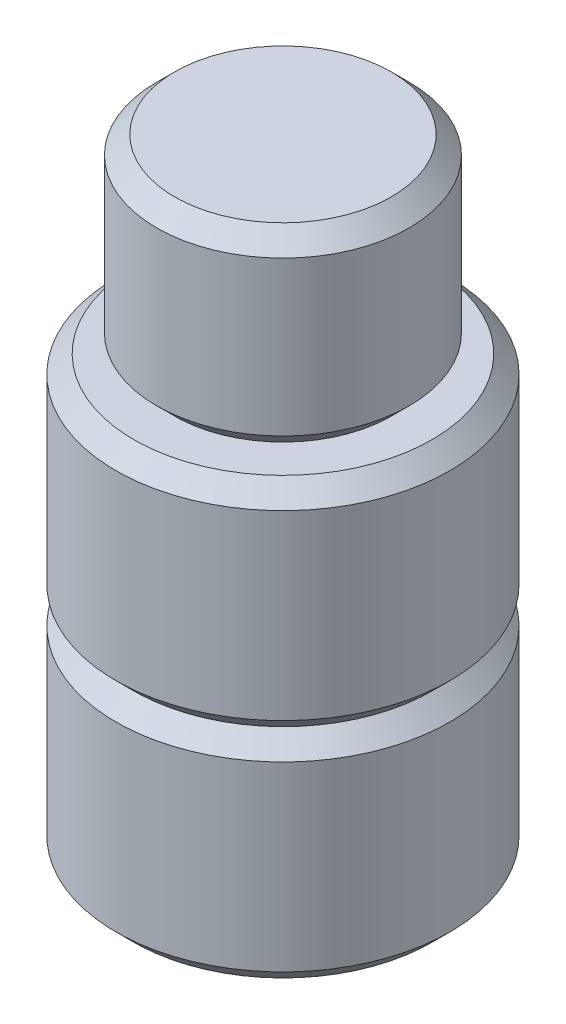
SolidWorks part; units mm, degrees
ref_plane "Front" through (0, 0, 0) normal (0, 0, 1) x (1, 0, 0)
ref_plane "Top" through (0, 0, 0) normal (0, 1, 0) x (1, 0, 0)
ref_plane "Right" through (0, 0, 0) normal (1, 0, 0) x (0, 0, -1)
sketch "Sketch1" plane through (0, 0, 0) normal (0, 0, 1) x (1, 0, 0)
  line L0 (0, 0) -> (0, 69.83) construction
  line L1 (0, 0) -> (16.65, 0)
  line L2 (16.65, 0) -> (18.65, 2)
  line L3 (18.65, 2) -> (18.65, 22.31)
  line L4 (18.65, 22.31) -> (16.65, 24.31)
  line L5 (16.65, 24.31) -> (18.65, 26.31)
  line L6 (18.65, 26.31) -> (18.65, 46.62)
  line L7 (18.65, 46.62) -> (16.65, 48.62)
  line L8 (16.65, 24.31) -> (0, 24.31) construction
  line L9 (16.65, 48.62) -> (0, 48.62) construction
  line L10 (16.65, 48.62) -> (12.1, 48.62)
  line L11 (12.1, 48.62) -> (14.1, 50.62)
  line L12 (14.1, 50.62) -> (14.1, 67.83)
  line L13 (14.1, 67.83) -> (12.1, 69.83)
  line L14 (12.1, 69.83) -> (0, 69.83)
  line L15 (0, 0) -> (0, 69.83)
  point P1 (14.1, 62.1285)
  point P13 (0, 63.0277)
  point P18 (18.65, 40.918)
  point P19 (16.65, 36.4987)
  dimension "D1" = 24.31
  dimension "D2" = 37.3
  dimension "D3" = 21.21
  dimension "D4" = 28.2
  dimension "D5" = 2
  dimension "D6" = 45
revolve "Revolve1" add sketch "Sketch1" angle 360 about L15
